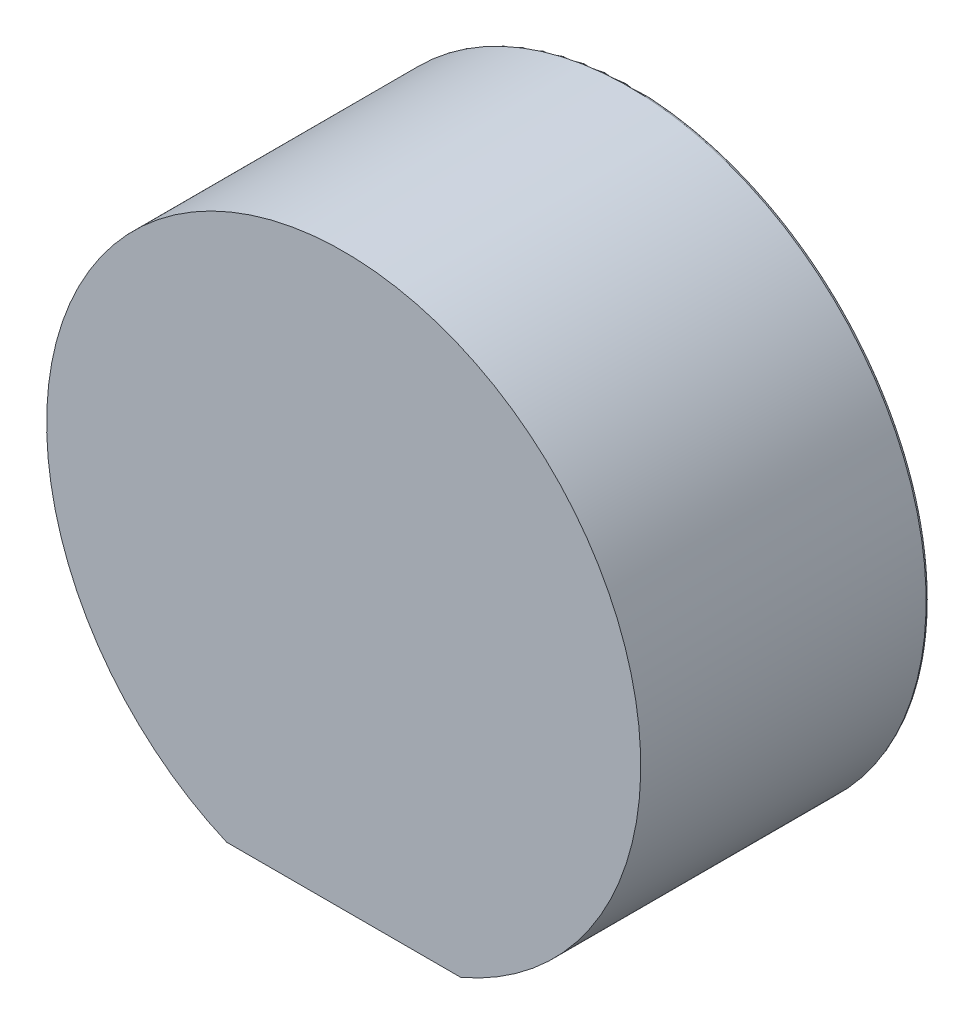
SolidWorks part; units mm, degrees
material "ABS"
ref_plane "Front Plane" through (0, 0, 0) normal (0, 0, 1) x (1, 0, 0)
ref_plane "Top Plane" through (0, 0, 0) normal (0, 1, 0) x (1, 0, 0)
ref_plane "Right Plane" through (0, 0, 0) normal (1, 0, 0) x (0, 0, -1)
sketch "Sketch1" plane through (0, 0, 0) normal (0, 0, 1) x (1, 0, 0)
  line L0 (-6.5, -15.1658) -> (6.5, -15.1658)
  circle A0 centre (0, 0) radius 16.5 construction
  arc A1 (-6.5, -15.1658) -> (6.6135, -15.1166) centre (0, 0) ccw construction
  arc A2 (-6.5, -15.1658) -> (6.5, -15.1658) centre (0, 0) cw
  dimension "D1" = 33
  dimension "D2" = 13
extrude "Boss-Extrude1" add sketch "Sketch1" against normal blind 8
sketch "Sketch5" plane through (0, 0, 0) normal (0, 0, 1) x (1, 0, 0)
sketch "Sketch7" plane through (0, 0, -8) normal (0, 0, -1) x (-1, 0, 0)
  circle A0 centre (0, 0) radius 16.5
extrude "Boss-Extrude2" add sketch "Sketch7" along normal blind 8 contours A0
fillet "Fillet1" radius 0.15 1 edges at (-16.5, 0, -16)
